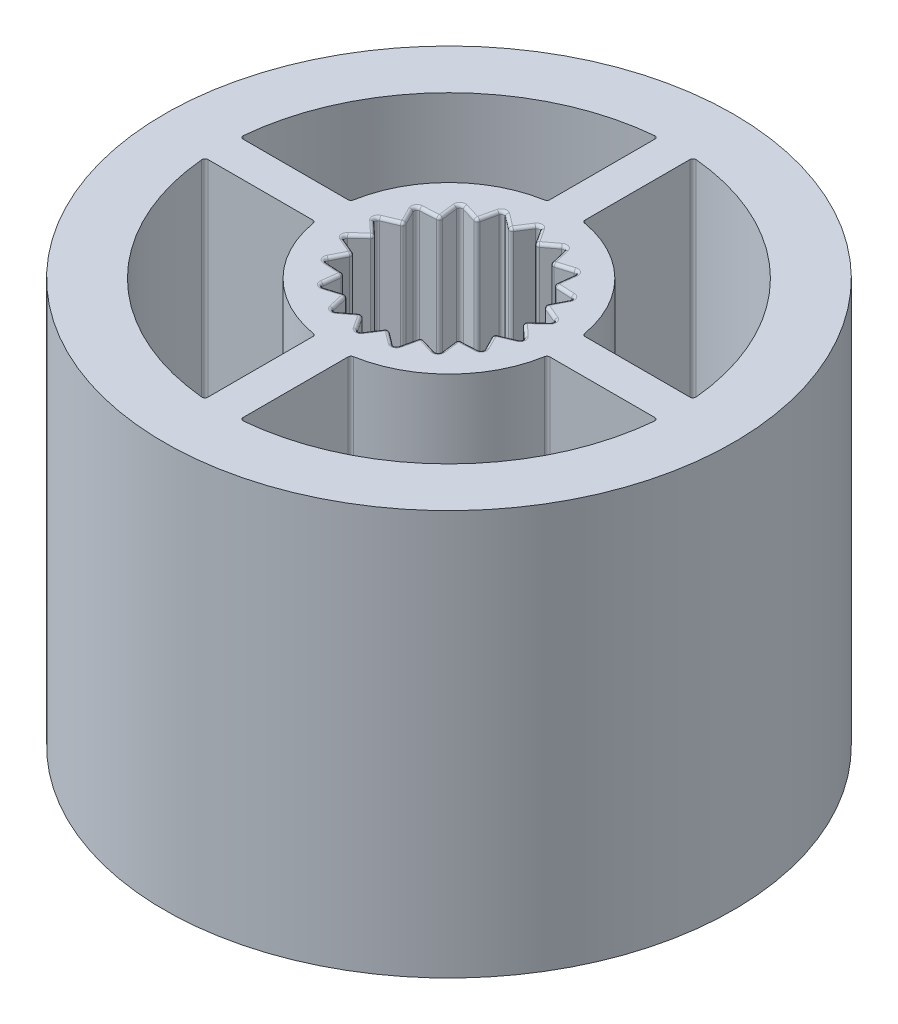
SolidWorks part; units mm, degrees
ref_plane "Front" through (0, 0, 0) normal (0, 0, 1) x (1, 0, 0)
ref_plane "Top" through (0, 0, 0) normal (0, 1, 0) x (1, 0, 0)
ref_plane "Right" through (0, 0, 0) normal (1, 0, 0) x (0, 0, -1)
sketch "Sketch1" plane through (0, 0, 0) normal (0, 1, 0) x (1, 0, 0)
  circle A0 centre (0, 0) radius 10
extrude "Boss-Extrude1" add sketch "Sketch1" along normal blind 16.8
sketch "Sketch8" plane through (0, 0, 0) normal (0, -1, 0) x (1, 0, 0)
  circle A0 centre (0, 0) radius 9.7
extrude "Cut-Extrude4" cut sketch "Sketch8" against normal offset from surface (16.3 mm away) 0.5 up to face at (0, 16.8, 10)
sketch "Sketch12" plane through (0, 0, 0) normal (0, -1, 0) x (1, 0, 0)
  circle A0 centre (0, 0) radius 7.75
  circle A1 centre (0, 0) radius 9.7
  circle A2 centre (0, 0) radius 9.7
  dimension "D1" = 0
extrude "Boss-Extrude6" add sketch "Sketch12" along normal blind 13.8
sketch "Sketch10" plane through (0, 0, 0) normal (0, -1, 0) x (1, 0, 0)
  line L0 (0, 0) -> (0, 3.1672) construction
  line L1 (0, 0) -> (0.5965, 3.3826) construction
  line L2 (1.0833, 2.9762) -> (0, 0) construction
  line L3 (0, 3.1672) -> (0.4391, 2.4901)
  line L4 (1.0833, 2.9762) -> (0.4391, 2.4901)
  line L5 (1.0833, 2.9762) -> (1.2643, 2.1898)
  line L6 (2.0359, 2.4262) -> (1.2643, 2.1898)
  line L7 (2.0359, 2.4262) -> (1.937, 1.6253)
  line L8 (2.7429, 1.5836) -> (1.937, 1.6253)
  line L9 (2.7429, 1.5836) -> (2.3761, 0.8648)
  line L10 (3.1191, 0.55) -> (2.3761, 0.8648)
  line L11 (3.1191, 0.55) -> (2.5286, 0)
  line L12 (3.1191, -0.55) -> (2.5286, 0)
  line L13 (3.1191, -0.55) -> (2.3761, -0.8648)
  line L14 (2.7429, -1.5836) -> (2.3761, -0.8648)
  line L15 (2.7429, -1.5836) -> (1.937, -1.6253)
  line L16 (2.0359, -2.4262) -> (1.937, -1.6253)
  line L17 (2.0359, -2.4262) -> (1.2643, -2.1898)
  line L18 (1.0833, -2.9762) -> (1.2643, -2.1898)
  line L19 (1.0833, -2.9762) -> (0.4391, -2.4901)
  line L20 (0, -3.1672) -> (0.4391, -2.4901)
  line L21 (0, -3.1672) -> (-0.4391, -2.4901)
  line L22 (-1.0833, -2.9762) -> (-0.4391, -2.4901)
  line L23 (-1.0833, -2.9762) -> (-1.2643, -2.1898)
  line L24 (-2.0359, -2.4262) -> (-1.2643, -2.1898)
  line L25 (-2.0359, -2.4262) -> (-1.937, -1.6253)
  line L26 (-2.7429, -1.5836) -> (-1.937, -1.6253)
  line L27 (-2.7429, -1.5836) -> (-2.3761, -0.8648)
  line L28 (-3.1191, -0.55) -> (-2.3761, -0.8648)
  line L29 (-3.1191, -0.55) -> (-2.5286, 0)
  line L30 (-3.1191, 0.55) -> (-2.5286, 0)
  line L31 (-3.1191, 0.55) -> (-2.3761, 0.8648)
  line L32 (-2.7429, 1.5836) -> (-2.3761, 0.8648)
  line L33 (-2.7429, 1.5836) -> (-1.937, 1.6253)
  line L34 (-2.0359, 2.4262) -> (-1.937, 1.6253)
  line L35 (-2.0359, 2.4262) -> (-1.2643, 2.1898)
  line L36 (-1.0833, 2.9762) -> (-1.2643, 2.1898)
  line L37 (-1.0833, 2.9762) -> (-0.4391, 2.4901)
  line L38 (0, 3.1672) -> (-0.4391, 2.4901)
  circle A0 centre (0, 0) radius 4
  circle A1 centre (0, 0) radius 2.6 construction
  point P9 (0, 0)
  point P14 (0, 0)
  point P18 (0, 0)
  point P22 (0, 0)
  point P26 (0, 0)
  point P30 (0, 0)
  point P34 (0, 0)
  point P38 (0, 0)
  point P42 (0, 0)
  point P46 (0, 0)
  point P50 (0, 0)
  point P54 (0, 0)
  point P58 (0, 0)
  point P62 (0, 0)
  point P66 (0, 0)
  point P70 (0, 0)
  point P74 (0, 0)
  point P78 (0, 0)
  point P79 (0, 0)
extrude "Boss-Extrude4" add sketch "Sketch10" along normal offset from surface (12.8 mm away) 1 contours A0 L3 L38 L37 L36 L35 L34 L33 L32 L31 L30 L29 L28 L27 L26 L25 L24 L23 L22 L21 L20 L19 L18 L17 L16 L15 L14 L13 L12 L11 L10 L9 L8 L7 L6 L5 L4 up to face at (0, -13.8, -9.7)
sketch "Sketch11" plane through (0, 0, 0) normal (0, -1, 0) x (1, 0, 0)
  line L0 (0, 0) -> (0, 9.7) construction
  line L1 (8.2675, 0.6) -> (8.2675, -0.6)
  line L2 (-0.6, 8.2675) -> (0.6, 8.2675)
  line L3 (-0.6, 8.2675) -> (-0.6, 3.3096)
  line L4 (-0.6, 3.3096) -> (0.6, 3.3096)
  line L5 (0.6, 8.2675) -> (0.6, 3.3096)
  line L6 (-0.6, 8.2675) -> (0.6, 3.3096) construction
  line L7 (-0.6, 3.3096) -> (0.6, 8.2675) construction
  line L8 (8.2675, 0.6) -> (3.3096, 0.6)
  line L9 (3.3096, 0.6) -> (3.3096, -0.6)
  line L10 (8.2675, -0.6) -> (3.3096, -0.6)
  line L11 (8.2675, 0.6) -> (3.3096, -0.6) construction
  line L12 (3.3096, 0.6) -> (8.2675, -0.6) construction
  line L13 (0.6, -8.2675) -> (-0.6, -8.2675)
  line L14 (0.6, -8.2675) -> (0.6, -3.3096)
  line L15 (0.6, -3.3096) -> (-0.6, -3.3096)
  line L16 (-0.6, -8.2675) -> (-0.6, -3.3096)
  line L17 (0.6, -8.2675) -> (-0.6, -3.3096) construction
  line L18 (0.6, -3.3096) -> (-0.6, -8.2675) construction
  line L19 (-8.2675, -0.6) -> (-8.2675, 0.6)
  line L20 (-8.2675, -0.6) -> (-3.3096, -0.6)
  line L21 (-3.3096, -0.6) -> (-3.3096, 0.6)
  line L22 (-8.2675, 0.6) -> (-3.3096, 0.6)
  line L23 (-8.2675, -0.6) -> (-3.3096, 0.6) construction
  line L24 (-3.3096, -0.6) -> (-8.2675, 0.6) construction
  circle A0 centre (0, 0) radius 9.7 construction
  point P6 (0, 5.7886)
  point P12 (0, 0)
  point P15 (5.7886, 0)
  point P20 (0, -5.7886)
  point P25 (-5.7886, 0)
  point P30 (0, 0)
  dimension "D1" = 4
extrude "Boss-Extrude5" add sketch "Sketch11" along normal offset from surface (12.3 mm away) 0.5 up to face at (0, -12.8, 0)
sketch "Sketch16" plane through (0, 0, 0) normal (0, 0, 1) x (1, 0, 0)
  line L1 (-10, 22.025) -> (10, 22.025)
  line L2 (-10, 22.025) -> (-10, 0)
  line L3 (-10, 0) -> (10, 0)
  line L4 (10, 22.025) -> (10, 0)
  line L5 (-10, 22.025) -> (10, 0) construction
  line L6 (-10, 0) -> (10, 22.025) construction
  point P0 (0, 11.0125)
extrude "Cut-Extrude5" cut sketch "Sketch16" against normal through all both and the other way through all
fillet "Fillet1" radius 0.1 141 edges at (3.9547, -6.15, -0.6) (3.9547, -6.15, 0.6) (-0.6, -6.15, -3.9547) (0.6, -6.15, -3.9547) (-3.9547, -6.15, 0.6) (-3.9547, -6.15, -0.6) (0.6, -6.15, 3.9547) (-0.6, -6.15, 3.9547) (1.937, -6.4, -1.6253) (2.0359, -6.4, -2.4262) (5.8407, -12.3, -0.6) (4, -12.3, 0) (5.8407, -12.3, 0.6) (-0.6, -12.3, -5.8407) (0, -12.3, -4) (0.6, -12.3, -5.8407) (-5.8407, -12.3, 0.6) (-4, -12.3, 0) (-5.8407, -12.3, -0.6) (0.6, -12.3, 5.8407) (0, -12.3, 4) (-0.6, -12.3, 5.8407) (0, -12.8, -4) (0.2195, -12.8, 2.8287) (-0.7612, -12.8, 2.7332) (-1.6501, -12.8, 2.308) (-2.3399, -12.8, 1.6045) (-2.7476, -12.8, 0.7074) (-2.8238, -12.8, -0.275) (-2.5595, -12.8, -1.2242) (-1.9864, -12.8, -2.0258) (-1.1738, -12.8, -2.583) (-0.2195, -12.8, -2.8287) (0.7612, -12.8, -2.7332) (1.6501, -12.8, -2.308) (1.9864, -12.8, -2.0258) (2.3399, -12.8, -1.6045) (2.7476, -12.8, -0.7074) (2.8238, -12.8, 0.275) (2.5595, -12.8, 1.2242) (1.9864, -12.8, 2.0258) (1.1738, -12.8, 2.583) (-2.3761, -6.4, 0.8648) (-2.5595, -12.8, 1.2242) (-2.7429, -6.4, 1.5836) (-2.5286, -6.4, 0) (-2.8238, -12.8, 0.275) (-3.1191, -6.4, 0.55) (-2.3761, -6.4, -0.8648) (-2.7476, -12.8, -0.7074) (-3.1191, -6.4, -0.55) (-1.937, -6.4, -1.6253) (-2.3399, -12.8, -1.6045) (-2.7429, -6.4, -1.5836) (-1.2643, -6.4, -2.1898) (-1.6501, -12.8, -2.308) (-2.0359, -6.4, -2.4262) (-0.4391, -6.4, -2.4901) (-0.7612, -12.8, -2.7332) (-1.0833, -6.4, -2.9762) (1.2643, -6.4, -2.1898) (1.1738, -12.8, -2.583) (1.0833, -6.4, -2.9762) (0.4391, -6.4, -2.4901) (0.2195, -12.8, -2.8287) (0, -6.4, -3.1672) (2.5286, -6.4, 0) (2.8238, -12.8, -0.275) (3.1191, -6.4, -0.55) (2.3761, -6.4, -0.8648) (2.5595, -12.8, -1.2242) (2.7429, -6.4, -1.5836) (2.3761, -6.4, 0.8648) (2.7476, -12.8, 0.7074) (3.1191, -6.4, 0.55) (1.937, -6.4, 1.6253) (2.3399, -12.8, 1.6045) (2.7429, -6.4, 1.5836) (1.2643, -6.4, 2.1898) (1.6501, -12.8, 2.308) (2.0359, -6.4, 2.4262) (0.4391, -6.4, 2.4901) (0.7612, -12.8, 2.7332) (1.0833, -6.4, 2.9762) (-0.4391, -6.4, 2.4901) (-0.2195, -12.8, 2.8287) (0, -6.4, 3.1672) (-1.2643, -6.4, 2.1898) (-1.1738, -12.8, 2.583) (-1.0833, -6.4, 2.9762) (-1.937, -6.4, 1.6253) (-1.9864, -12.8, 2.0258) (-2.0359, -6.4, 2.4262) (1.6501, 0, -2.308) (-2.3399, 0, 1.6045) (-2.7476, 0, 0.7074) (-2.8238, 0, -0.275) (-2.5595, 0, -1.2242) (-1.9864, 0, -2.0258) (-1.1738, 0, -2.583) (0.7612, 0, -2.7332) (-0.2195, 0, -2.8287) (2.7476, 0, -0.7074) (2.3399, 0, -1.6045) (2.8238, 0, 0.275) (2.5595, 0, 1.2242) (1.9864, 0, 2.0258) (1.1738, 0, 2.583) (0.2195, 0, 2.8287) (-0.7612, 0, 2.7332) (-1.6501, 0, 2.308) (1.9864, 0, -2.0258) (-2.5595, 0, 1.2242) (-2.8238, 0, 0.275) (-2.7476, 0, -0.7074) (-2.3399, 0, -1.6045) (-1.6501, 0, -2.308) (-0.7612, 0, -2.7332) (1.1738, 0, -2.583) (0.2195, 0, -2.8287) (2.8238, 0, -0.275) (2.5595, 0, -1.2242) (2.7476, 0, 0.7074) (2.3399, 0, 1.6045) (1.6501, 0, 2.308) (0.7612, 0, 2.7332) (-0.2195, 0, 2.8287) (-1.1738, 0, 2.583) (-1.9864, 0, 2.0258) (0.6, -6.15, 7.7267) (-0.6, -6.15, 7.7267) (0.6, -6.15, -7.7267) (-0.6, -6.15, -7.7267) (-7.7267, -6.15, -0.6) (-7.7267, -6.15, 0.6) (7.7267, -6.15, 0.6) (7.7267, -6.15, -0.6) (0, -12.3, 7.75) (0, -12.3, -7.75) (-7.75, -12.3, 0) (7.75, -12.3, 0)
